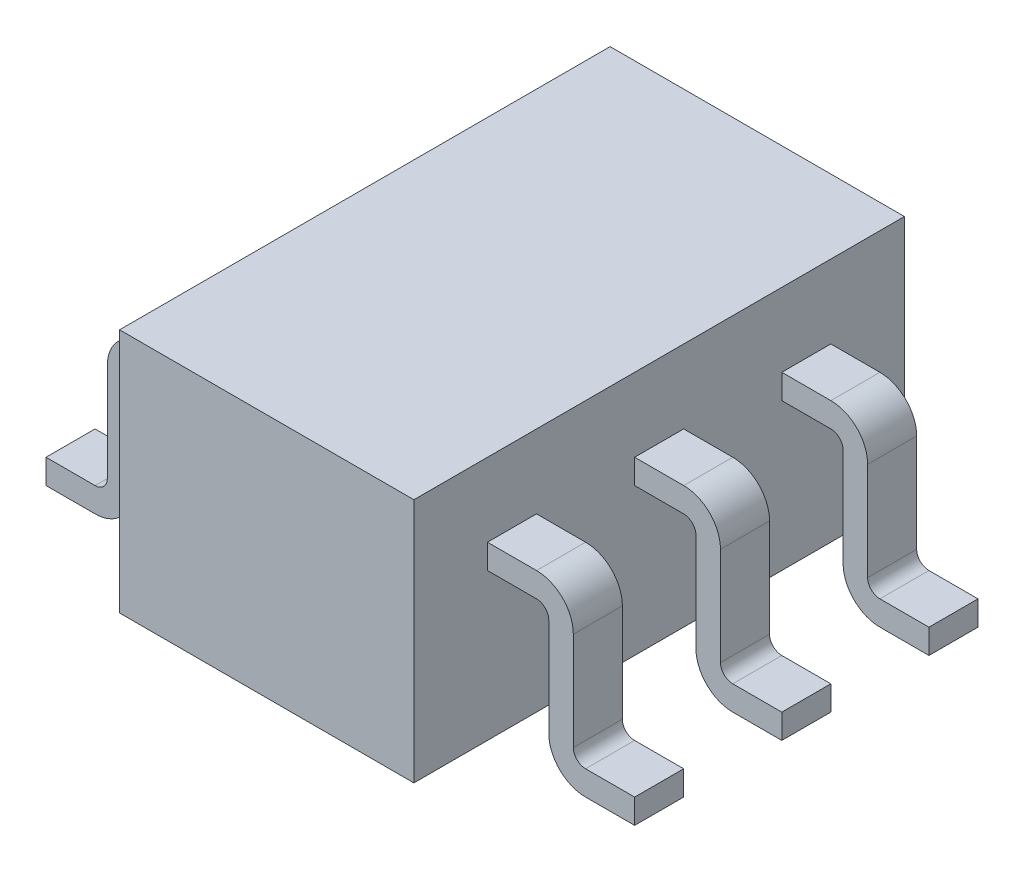
SolidWorks part; units mm, degrees
ref_plane "Front Plane" through (0, 0, 0) normal (0, 0, 1) x (1, 0, 0)
ref_plane "Top Plane" through (0, 0, 0) normal (0, 1, 0) x (1, 0, 0)
ref_plane "Right Plane" through (0, 0, 0) normal (1, 0, 0) x (0, 0, -1)
sketch "BaseS" plane through (0, 0, 0) normal (0, 1, 0) x (1, 0, 0)
  line L1 (-0.6, 1) -> (0.6, 1)
  line L2 (-0.6, 1) -> (-0.6, -1)
  line L3 (-0.6, -1) -> (0.6, -1)
  line L4 (0.6, 1) -> (0.6, -1)
  line L5 (-0.6, 1) -> (0.6, -1) construction
  line L6 (-0.6, -1) -> (0.6, 1) construction
  point P0 (0, 0)
  dimension "Length" = 2
  dimension "Width" = 1.2
extrude "Base" add sketch "BaseS" along normal mid plane 1
ref_plane "LegRP" through (0, 0, 0.6) normal (0, 0, 1) x (1, 0, 0)
sketch "MiddleLegS" plane through (0, 0, 0.6) normal (0, 0, 1) x (1, 0, 0)
  line L0 (0.6, 0.5) -> (0.6, -0.5) construction
  line L1 (-0.6, -0.5) -> (0.6, -0.5) construction
  line L3 (1.2, -0.45) -> (1, -0.45)
  line L4 (0.9, -0.35) -> (0.9, 0.05)
  line L5 (0.6, 0.15) -> (0.8, 0.15)
  line L6 (0.6, 0.5) -> (0.6, -0.5) construction
  arc A2 (0.9, -0.35) -> (1, -0.45) centre (1, -0.35) ccw
  arc A3 (0.9, 0.05) -> (0.8, 0.15) centre (0.8, 0.05) ccw
  dimension "D3" = 0.1
  dimension "D4" = 0.1
  dimension "D1" = 0.2
  dimension "D2" = 0.2
  dimension "D5" = 0.05
  dimension "Height" = 0.6
extrude "MiddleLeg" add sketch "MiddleLegS" along normal mid plane 0.2 thin contours L5 A3 L4 A2 L3 thin type mid plane wall 0.1
pattern_linear "LPattern1" count 3 spacing 0.6 along (0, 0, -1) of "MiddleLeg"
mirror "Mirror1" about plane through (0, 0, 0) normal (1, 0, 0) of "LPattern1", "MiddleLeg"
